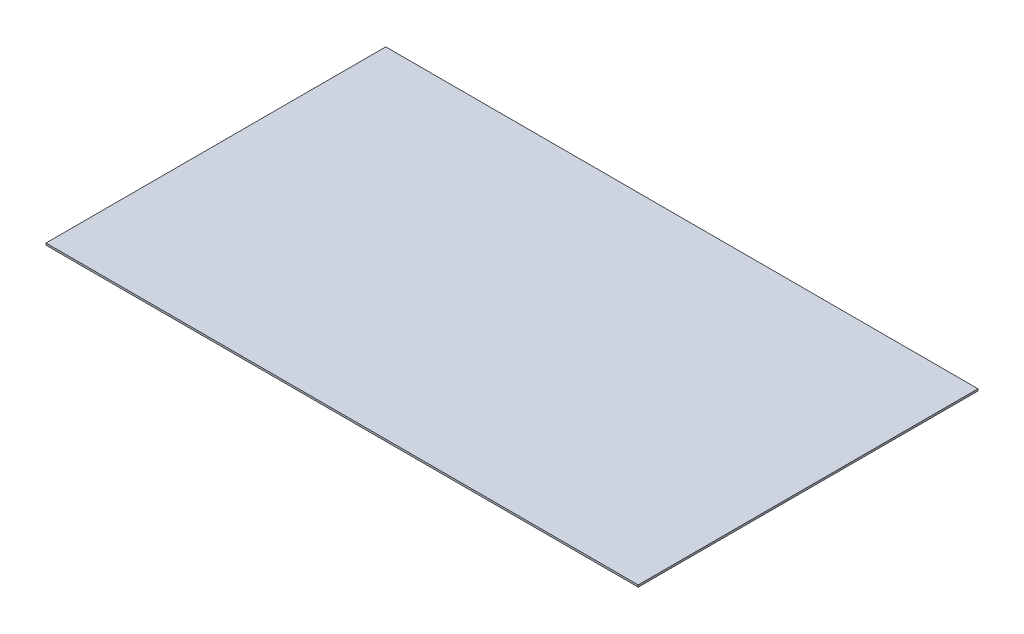
SolidWorks part; units mm, degrees
material "solar panel"
ref_plane "Front Plane" through (0, 0, 0) normal (0, 0, 1) x (1, 0, 0)
ref_plane "Top Plane" through (0, 0, 0) normal (0, 1, 0) x (1, 0, 0)
ref_plane "Right Plane" through (0, 0, 0) normal (1, 0, 0) x (0, 0, -1)
sketch "Sketch1" plane through (0, 0, 0) normal (0, 1, 0) x (1, 0, 0)
  line L1 (34.8625, 20) -> (-34.8625, 20)
  line L2 (34.8625, 20) -> (34.8625, -20)
  line L3 (34.8625, -20) -> (-34.8625, -20)
  line L4 (-34.8625, 20) -> (-34.8625, -20)
  line L5 (34.8625, 20) -> (-34.8625, -20) construction
  line L6 (34.8625, -20) -> (-34.8625, 20) construction
  point P0 (0, 0)
  dimension "D1" = 69.725
  dimension "D2" = 40
extrude "Boss-Extrude1" add sketch "Sketch1" along normal mid plane 0.225
